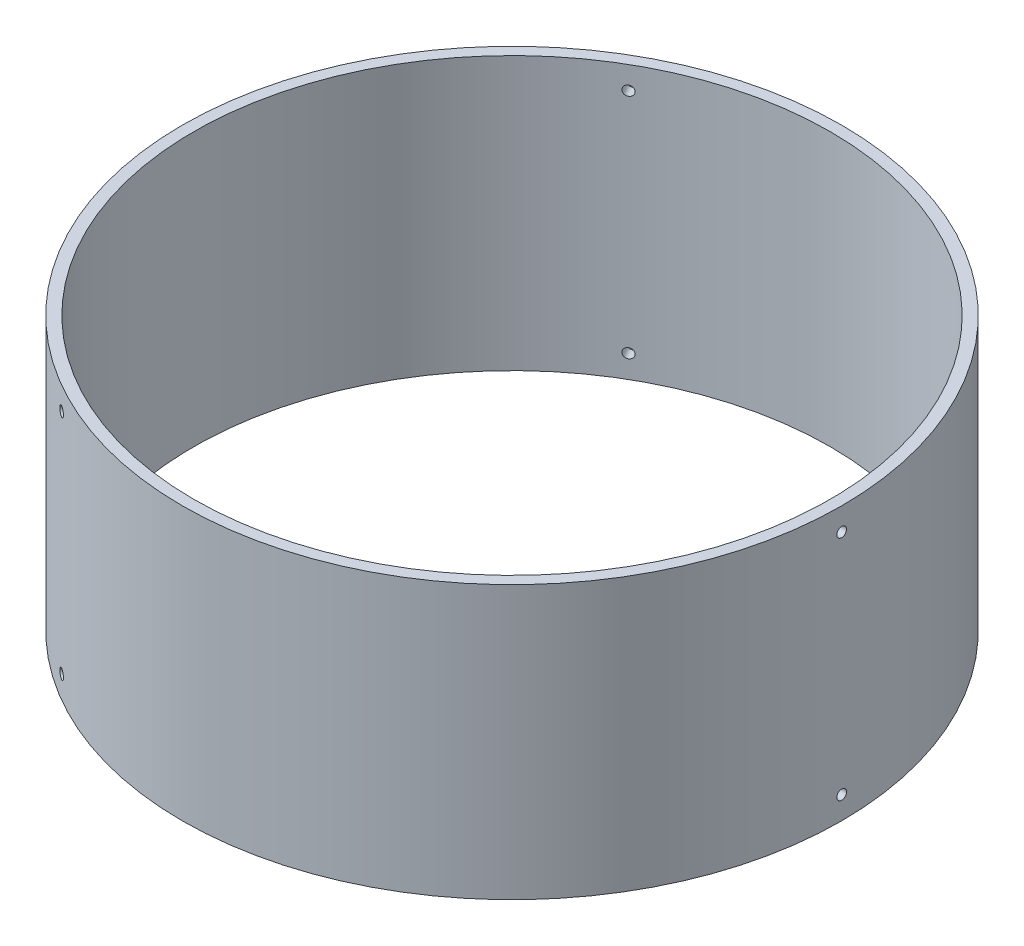
SolidWorks part; units mm, degrees
material "Acrylic (Medium-high impact)"
ref_plane "Front Plane" through (0, 0, 0) normal (0, 0, 1) x (1, 0, 0)
ref_plane "Top Plane" through (0, 0, 0) normal (0, 1, 0) x (1, 0, 0)
ref_plane "Right Plane" through (0, 0, 0) normal (1, 0, 0) x (0, 0, -1)
sketch "Sketch1" plane through (0, 0, 0) normal (0, 1, 0) x (1, 0, 0)
  circle A0 centre (0, 0) radius 92.075
  circle A1 centre (0, 0) radius 88.9
  dimension "D1" = 184.15
  dimension "D2" = 177.8
extrude "Boss-Extrude1" add sketch "Sketch1" along normal mid plane 76.2
ref_plane "Plane1" through (92.075, 0, 0) normal (1, 0, 0) x (0, 0, -1)
sketch "Sketch3" plane through (92.075, 0, 0) normal (1, 0, 0) x (0, 0, -1)
  line L0 (0, 41.91) -> (0, -41.91) construction
  line L1 (88.9, 38.1) -> (-88.9, 38.1) construction
  line L2 (-92.075, -38.1) -> (92.075, -38.1) construction
  circle A0 centre (0, -31.75) radius 1.3526
  circle A1 centre (0, 31.75) radius 1.3526
  dimension "D1" = 6.35
  dimension "D2" = 2.7051
  dimension "D3" = 2.7051
  dimension "D4" = 6.35
extrude "Cut-Extrude1" cut sketch "Sketch3" against normal blind 34.798
pattern_circular "CirPattern1" count 3 over 360 about axis through (0, 38.1, 0) along (0, -1, 0) of "Cut-Extrude1"
